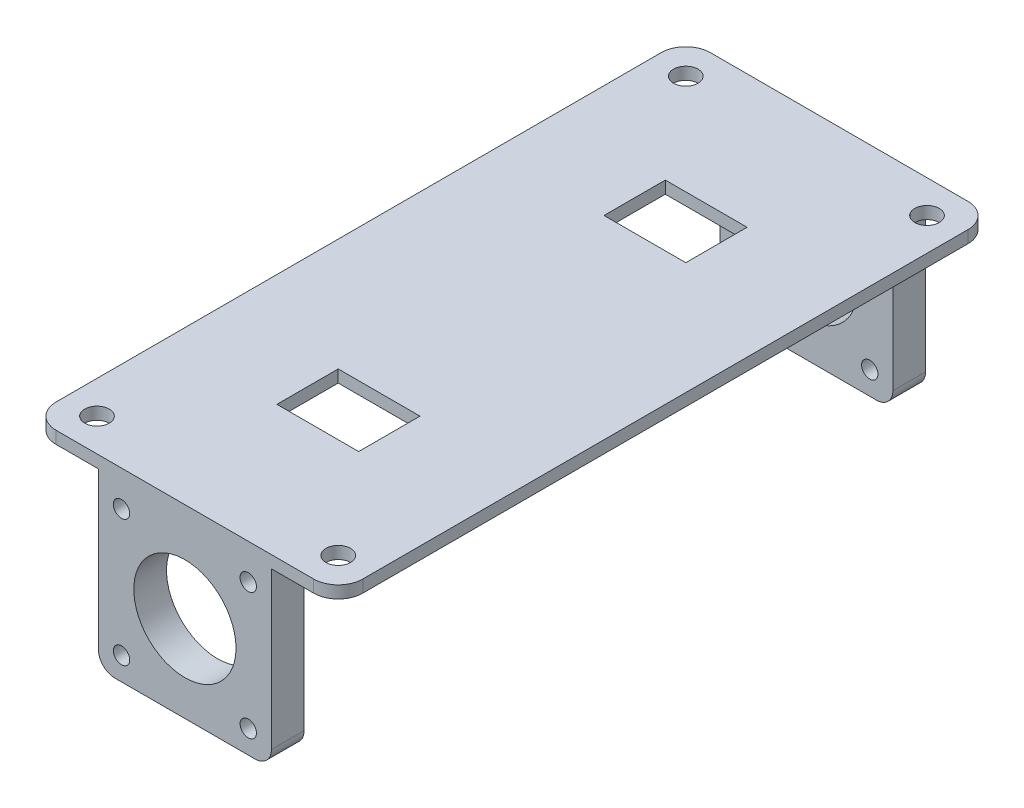
SolidWorks part; units mm, degrees
ref_plane "Alzado" through (0, 0, 0) normal (0, 0, 1) x (1, 0, 0)
ref_plane "Planta" through (0, 0, 0) normal (0, 1, 0) x (1, 0, 0)
ref_plane "Vista lateral" through (0, 0, 0) normal (1, 0, 0) x (0, 0, -1)
sketch "Croquis1" plane through (0, 0, 0) normal (0, 0, 1) x (1, 0, 0)
  line L1 (21.15, 21.15) -> (-21.15, 21.15)
  line L2 (21.15, 21.15) -> (21.15, -21.15)
  line L3 (21.15, -21.15) -> (-21.15, -21.15)
  line L4 (-21.15, 21.15) -> (-21.15, -21.15)
  line L5 (21.15, 21.15) -> (-21.15, -21.15) construction
  line L6 (21.15, -21.15) -> (-21.15, 21.15) construction
  circle A0 centre (0, 0) radius 12.5
  circle A1 centre (-15.5, 15.5) radius 2
  circle A2 centre (15.5, 15.5) radius 2
  circle A3 centre (15.5, -15.5) radius 2
  circle A4 centre (-15.5, -15.5) radius 2
  point P0 (0, 0)
  point P13 (0, 0)
  point P16 (0, 0)
  point P19 (0, 0)
  point P22 (0, 0)
  dimension "D3" = 25
  dimension "D4" = 4
  dimension "D6" = 31
  dimension "D1" = 42.3
  dimension "D2" = 42.3
  dimension "D7" = 31
  dimension "D5" = 4
extrude "Saliente-Extruir2" add sketch "Croquis1" along normal blind 8
sketch "Croquis3" plane through (0, 21.15, 0) normal (0, 1, 0) x (1, 0, 0)
  line L0 (0, 0) -> (0, 72) construction
  line L1 (21.15, -8) -> (-21.15, -8) construction
  line L2 (37.5, 72) -> (-37.5, 72)
  line L3 (37.5, 72) -> (37.5, -8)
  line L4 (37.5, -8) -> (-37.5, -8)
  line L5 (-37.5, 72) -> (-37.5, -8)
  line L6 (37.5, 72) -> (-37.5, -8) construction
  line L7 (37.5, -8) -> (-37.5, 72) construction
  line L8 (21.15, 0) -> (-21.15, 0) construction
  line L9 (10, 39.5) -> (-10, 39.5)
  line L10 (10, 39.5) -> (10, 24.5)
  line L11 (10, 24.5) -> (-10, 24.5)
  line L12 (-10, 39.5) -> (-10, 24.5)
  line L13 (10, 39.5) -> (-10, 24.5) construction
  line L14 (10, 24.5) -> (-10, 39.5) construction
  circle A0 centre (-29.5, 0) radius 3
  circle A1 centre (29.5, 0) radius 3
  point P3 (0, 32)
  point P14 (0, 32)
  dimension "D3" = 6
  dimension "D1" = 80
  dimension "D2" = 75
  dimension "D4" = 8
  dimension "D5" = 20
  dimension "D6" = 15
  dimension "D7" = 32
  dimension "D8" = 8
extrude "Saliente-Extruir3" add sketch "Croquis3" along normal blind 3
ref_plane "Plano1" through (0, 0, -72) normal (0, 0, -1) x (-1, 0, 0)
mirror "Simetría10" about plane through (0, 0, -72) normal (0, 0, -1) of "Saliente-Extruir3"
mirror "Simetría12" about plane through (0, 0, -72) normal (0, 0, -1) of "Saliente-Extruir2"
fillet "Redondeo1" radius 4 4 edges at (-21.15, -21.15, 4) (21.15, -21.15, 4) (21.15, -21.15, -148) (-21.15, -21.15, -148)
fillet "Redondeo3" radius 6 4 edges at (37.5, 22.65, 8) (-37.5, 22.65, 8) (-37.5, 22.65, -152) (37.5, 22.65, -152)
sketch "Croquis4" plane through (0, 24.15, 0) normal (0, 1, 0) x (1, 0, 0)
  line L0 (10, 104.5) -> (-10, 104.5) construction
  line L1 (10, 39.5) -> (-10, 39.5) construction
  dimension "D1" = 65
